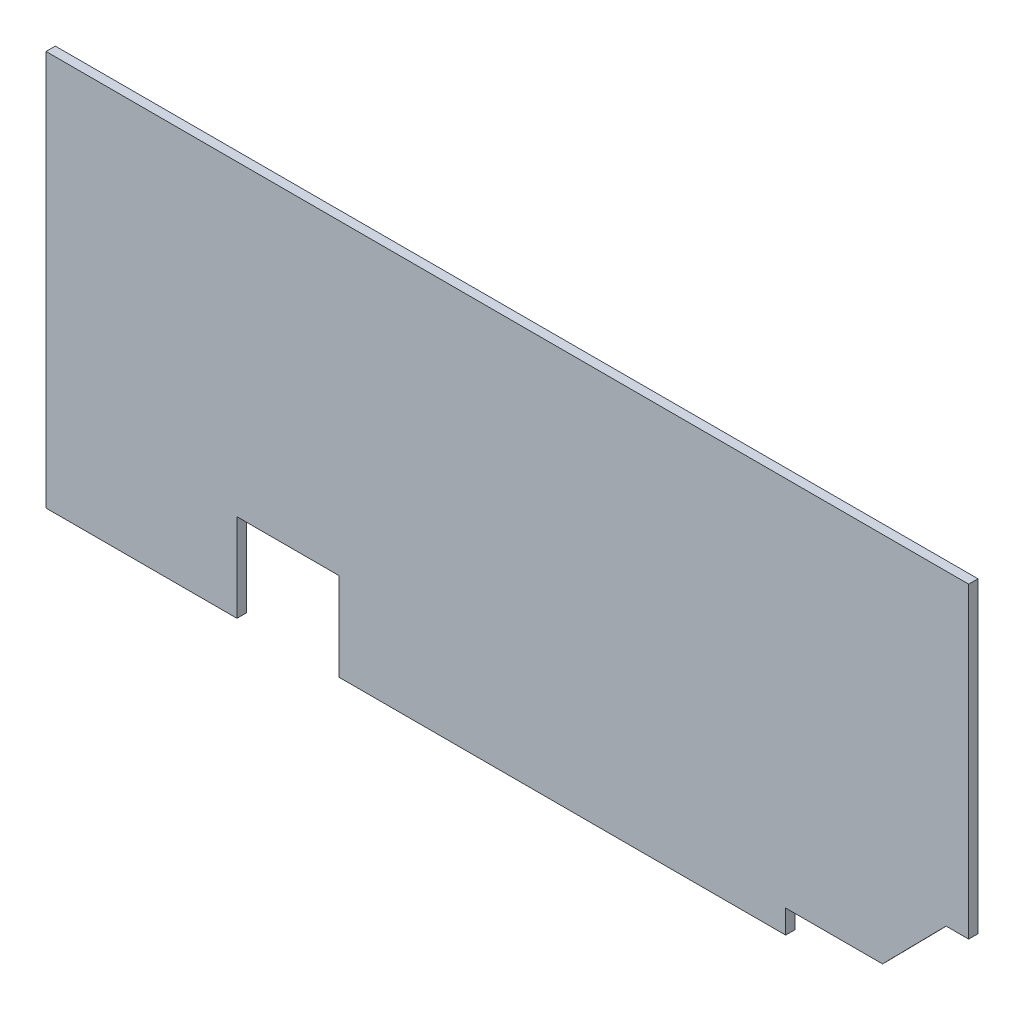
SolidWorks part; units mm, degrees
ref_plane "Front Plane" through (0, 0, 0) normal (0, 0, 1) x (1, 0, 0)
ref_plane "Top Plane" through (0, 0, 0) normal (0, 1, 0) x (1, 0, 0)
ref_plane "Right Plane" through (0, 0, 0) normal (1, 0, 0) x (0, 0, -1)
sketch "Sketch1" plane through (0, 0, 0) normal (0, 0, 1) x (1, 0, 0)
  line L1 (-268.4008, 107.4341) -> (46.0496, 107.4341)
  line L2 (-268.4008, 107.4341) -> (-268.4008, -27.3409)
  line L9 (-268.4008, -27.3409) -> (-203.3208, -27.3409)
  line L10 (-203.3208, -27.3409) -> (-203.3208, 2.6591)
  line L11 (-203.3208, 2.6591) -> (-168.5664, 2.6591)
  line L12 (-168.5664, 2.6591) -> (-168.5664, -27.3409)
  line L14 (-168.5664, -27.3409) -> (-16.3208, -27.3409)
  line L15 (46.0496, 2.6591) -> (46.0496, 107.4341)
  line L16 (147.6496, -27.3409) -> (-268.4304, -27.3409) construction
  line L17 (-16.3208, -27.3409) -> (-16.3208, -19.3409)
  line L18 (-16.3208, -19.3409) -> (16.6792, -19.3409)
  line L19 (16.6792, -19.3409) -> (38.3417, 2.6591)
  line L20 (38.3417, 2.6591) -> (46.0496, 2.6591)
  line L21 (39.7147, 2.6591) -> (81.4792, 2.6591) construction
extrude "Boss-Extrude1" add sketch "Sketch1" along normal blind 3.175
